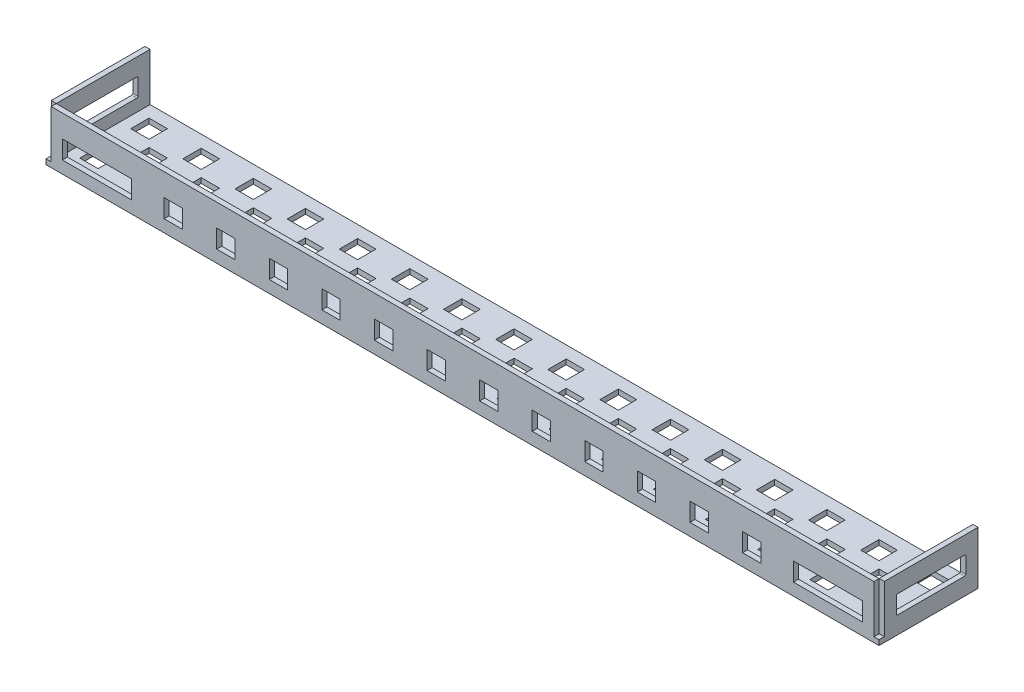
SolidWorks part; units mm, degrees
ref_plane "Front Plane" through (0, 0, 0) normal (0, 0, 1) x (1, 0, 0)
ref_plane "Top Plane" through (0, 0, 0) normal (0, 1, 0) x (1, 0, 0)
ref_plane "Right Plane" through (0, 0, 0) normal (1, 0, 0) x (0, 0, -1)
sketch "Sketch1" plane through (0, 0, 0) normal (0, 1, 0) x (1, 0, 0)
  line L0 (0, 0) -> (0, 23)
  line L1 (0, 23) -> (-204.5, 23)
  line L2 (-204.5, 23) -> (-204.5, 0)
  line L3 (-204.5, 0) -> (0, 0)
  point P13 (0, 0)
  point P14 (0, 0)
  dimension "D1" = 23
  dimension "D2" = 204.5
extrude "Boss-Extrude1" add sketch "Sketch1" along normal blind 1.25
sketch "Sketch2" plane through (0, 1.25, 0) normal (0, 1, 0) x (1, 0, 0)
  line L0 (-204.5, 0) -> (0, 0) construction
  line L1 (-204.5, 23) -> (-203.25, 23)
  line L2 (-204.5, 23) -> (-204.5, 0)
  line L3 (-204.5, 0) -> (-203.25, 0)
  line L4 (-203.25, 23) -> (-203.25, 0)
  line L6 (0, 23) -> (-1.25, 23)
  line L7 (0, 23) -> (0, 0)
  line L8 (0, 0) -> (-1.25, 0)
  line L9 (-1.25, 23) -> (-1.25, 0)
  dimension "D1" = 1.25
  dimension "D2" = 1.25
extrude "Boss-Extrude2" add sketch "Sketch2" along normal blind 11.75
sketch "Sketch3" plane through (0, 0, 0) normal (1, 0, 0) x (0, 0, -1)
  line L0 (0, 13) -> (23, 13) construction
  line L1 (3.25, 8.75) -> (19.75, 8.75)
  line L2 (3, 8.5) -> (3, 4.5)
  line L3 (3.25, 4.25) -> (19.75, 4.25)
  line L4 (20, 8.5) -> (20, 4.5)
  line L5 (0, 13) -> (0, 0) construction
  arc A0 (3.25, 8.75) -> (3, 8.5) centre (3.25, 8.5) ccw
  arc A1 (20, 8.5) -> (19.75, 8.75) centre (19.75, 8.5) ccw
  arc A2 (19.75, 4.25) -> (20, 4.5) centre (19.75, 4.5) ccw
  arc A3 (3.25, 4.25) -> (3, 4.5) centre (3.25, 4.5) cw
  point P4 (11.5, 8.75)
  point P7 (11.5, 13)
  point P8 (3, 6.5)
  point P11 (0, 6.5)
  point P14 (3, 8.75)
  point P17 (20, 8.75)
  dimension "D3" = 0.25
  dimension "D4" = 0.25
  dimension "D1" = 17
  dimension "D2" = 4.5
extrude "Cut-Extrude1" cut sketch "Sketch3" against normal blind 220
sketch "Sketch4" plane through (0, 0, 0) normal (0, -1, 0) x (1, 0, 0)
  line L0 (0, -23) -> (-204.5, -23) construction
  line L1 (-200.5, -3) -> (-196, -3)
  line L2 (-200.5, -3) -> (-200.5, -7.5)
  line L3 (-200.5, -7.5) -> (-196, -7.5)
  line L4 (-196, -3) -> (-196, -7.5)
  line L5 (-200.5, -15.5) -> (-196, -15.5)
  line L6 (-200.5, -15.5) -> (-200.5, -20)
  line L7 (-200.5, -20) -> (-196, -20)
  line L8 (-196, -15.5) -> (-196, -20)
  line L9 (-204.5, -23) -> (-204.5, 0) construction
  line L10 (-187.7, -3) -> (-183.2, -3)
  line L11 (-194.25, -9.25) -> (-189.75, -9.25)
  line L12 (-194.25, -9.25) -> (-194.25, -13.75)
  line L13 (-194.25, -13.75) -> (-189.75, -13.75)
  line L14 (-189.75, -9.25) -> (-189.75, -13.75)
  line L15 (-187.7, -3) -> (-187.7, -7.5)
  line L16 (-187.7, -7.5) -> (-183.2, -7.5)
  line L17 (-183.2, -3) -> (-183.2, -7.5)
  line L18 (-187.7, -15.5) -> (-183.2, -15.5)
  line L19 (-187.7, -15.5) -> (-187.7, -20)
  line L20 (-187.7, -20) -> (-183.2, -20)
  line L21 (-183.2, -15.5) -> (-183.2, -20)
  line L22 (-181.45, -9.25) -> (-176.95, -9.25)
  line L23 (-181.45, -9.25) -> (-181.45, -13.75)
  line L24 (-181.45, -13.75) -> (-176.95, -13.75)
  line L25 (-176.95, -9.25) -> (-176.95, -13.75)
  line L26 (-174.9, -3) -> (-170.4, -3)
  line L27 (-174.9, -3) -> (-174.9, -7.5)
  line L28 (-174.9, -7.5) -> (-170.4, -7.5)
  line L29 (-170.4, -3) -> (-170.4, -7.5)
  line L30 (-174.9, -15.5) -> (-170.4, -15.5)
  line L31 (-174.9, -15.5) -> (-174.9, -20)
  line L32 (-174.9, -20) -> (-170.4, -20)
  line L33 (-170.4, -15.5) -> (-170.4, -20)
  line L34 (-168.65, -9.25) -> (-164.15, -9.25)
  line L35 (-168.65, -9.25) -> (-168.65, -13.75)
  line L36 (-168.65, -13.75) -> (-164.15, -13.75)
  line L37 (-164.15, -9.25) -> (-164.15, -13.75)
  line L38 (-162.1, -3) -> (-157.6, -3)
  line L39 (-162.1, -3) -> (-162.1, -7.5)
  line L40 (-162.1, -7.5) -> (-157.6, -7.5)
  line L41 (-157.6, -3) -> (-157.6, -7.5)
  line L42 (-162.1, -15.5) -> (-157.6, -15.5)
  line L43 (-162.1, -15.5) -> (-162.1, -20)
  line L44 (-162.1, -20) -> (-157.6, -20)
  line L45 (-157.6, -15.5) -> (-157.6, -20)
  line L46 (-155.85, -9.25) -> (-151.35, -9.25)
  line L47 (-155.85, -9.25) -> (-155.85, -13.75)
  line L48 (-155.85, -13.75) -> (-151.35, -13.75)
  line L49 (-151.35, -9.25) -> (-151.35, -13.75)
  line L50 (-149.3, -3) -> (-144.8, -3)
  line L51 (-149.3, -3) -> (-149.3, -7.5)
  line L52 (-149.3, -7.5) -> (-144.8, -7.5)
  line L53 (-144.8, -3) -> (-144.8, -7.5)
  line L54 (-149.3, -15.5) -> (-144.8, -15.5)
  line L55 (-149.3, -15.5) -> (-149.3, -20)
  line L56 (-149.3, -20) -> (-144.8, -20)
  line L57 (-144.8, -15.5) -> (-144.8, -20)
  line L58 (-143.05, -9.25) -> (-138.55, -9.25)
  line L59 (-143.05, -9.25) -> (-143.05, -13.75)
  line L60 (-143.05, -13.75) -> (-138.55, -13.75)
  line L61 (-138.55, -9.25) -> (-138.55, -13.75)
  line L62 (-136.5, -3) -> (-132, -3)
  line L63 (-136.5, -3) -> (-136.5, -7.5)
  line L64 (-136.5, -7.5) -> (-132, -7.5)
  line L65 (-132, -3) -> (-132, -7.5)
  line L66 (-136.5, -15.5) -> (-132, -15.5)
  line L67 (-136.5, -15.5) -> (-136.5, -20)
  line L68 (-136.5, -20) -> (-132, -20)
  line L69 (-132, -15.5) -> (-132, -20)
  line L70 (-130.25, -9.25) -> (-125.75, -9.25)
  line L71 (-130.25, -9.25) -> (-130.25, -13.75)
  line L72 (-130.25, -13.75) -> (-125.75, -13.75)
  line L73 (-125.75, -9.25) -> (-125.75, -13.75)
  line L74 (-123.7, -3) -> (-119.2, -3)
  line L75 (-123.7, -3) -> (-123.7, -7.5)
  line L76 (-123.7, -7.5) -> (-119.2, -7.5)
  line L77 (-119.2, -3) -> (-119.2, -7.5)
  line L78 (-123.7, -15.5) -> (-119.2, -15.5)
  line L79 (-123.7, -15.5) -> (-123.7, -20)
  line L80 (-123.7, -20) -> (-119.2, -20)
  line L81 (-119.2, -15.5) -> (-119.2, -20)
  line L82 (-117.45, -9.25) -> (-112.95, -9.25)
  line L83 (-117.45, -9.25) -> (-117.45, -13.75)
  line L84 (-117.45, -13.75) -> (-112.95, -13.75)
  line L85 (-112.95, -9.25) -> (-112.95, -13.75)
  line L86 (-110.9, -3) -> (-106.4, -3)
  line L87 (-110.9, -3) -> (-110.9, -7.5)
  line L88 (-110.9, -7.5) -> (-106.4, -7.5)
  line L89 (-106.4, -3) -> (-106.4, -7.5)
  line L90 (-110.9, -15.5) -> (-106.4, -15.5)
  line L91 (-110.9, -15.5) -> (-110.9, -20)
  line L92 (-110.9, -20) -> (-106.4, -20)
  line L93 (-106.4, -15.5) -> (-106.4, -20)
  line L94 (-104.65, -9.25) -> (-100.15, -9.25)
  line L95 (-104.65, -9.25) -> (-104.65, -13.75)
  line L96 (-104.65, -13.75) -> (-100.15, -13.75)
  line L97 (-100.15, -9.25) -> (-100.15, -13.75)
  line L98 (-98.1, -3) -> (-93.6, -3)
  line L99 (-98.1, -3) -> (-98.1, -7.5)
  line L100 (-98.1, -7.5) -> (-93.6, -7.5)
  line L101 (-93.6, -3) -> (-93.6, -7.5)
  line L102 (-98.1, -15.5) -> (-93.6, -15.5)
  line L103 (-98.1, -15.5) -> (-98.1, -20)
  line L104 (-98.1, -20) -> (-93.6, -20)
  line L105 (-93.6, -15.5) -> (-93.6, -20)
  line L106 (-91.85, -9.25) -> (-87.35, -9.25)
  line L107 (-91.85, -9.25) -> (-91.85, -13.75)
  line L108 (-91.85, -13.75) -> (-87.35, -13.75)
  line L109 (-87.35, -9.25) -> (-87.35, -13.75)
  line L110 (-85.3, -3) -> (-80.8, -3)
  line L111 (-85.3, -3) -> (-85.3, -7.5)
  line L112 (-85.3, -7.5) -> (-80.8, -7.5)
  line L113 (-80.8, -3) -> (-80.8, -7.5)
  line L114 (-85.3, -15.5) -> (-80.8, -15.5)
  line L115 (-85.3, -15.5) -> (-85.3, -20)
  line L116 (-85.3, -20) -> (-80.8, -20)
  line L117 (-80.8, -15.5) -> (-80.8, -20)
  line L118 (-79.05, -9.25) -> (-74.55, -9.25)
  line L119 (-79.05, -9.25) -> (-79.05, -13.75)
  line L120 (-79.05, -13.75) -> (-74.55, -13.75)
  line L121 (-74.55, -9.25) -> (-74.55, -13.75)
  line L122 (-72.5, -3) -> (-68, -3)
  line L123 (-72.5, -3) -> (-72.5, -7.5)
  line L124 (-72.5, -7.5) -> (-68, -7.5)
  line L125 (-68, -3) -> (-68, -7.5)
  line L126 (-72.5, -15.5) -> (-68, -15.5)
  line L127 (-72.5, -15.5) -> (-72.5, -20)
  line L128 (-72.5, -20) -> (-68, -20)
  line L129 (-68, -15.5) -> (-68, -20)
  line L130 (-66.25, -9.25) -> (-61.75, -9.25)
  line L131 (-66.25, -9.25) -> (-66.25, -13.75)
  line L132 (-66.25, -13.75) -> (-61.75, -13.75)
  line L133 (-61.75, -9.25) -> (-61.75, -13.75)
  line L134 (-59.7, -3) -> (-55.2, -3)
  line L135 (-59.7, -3) -> (-59.7, -7.5)
  line L136 (-59.7, -7.5) -> (-55.2, -7.5)
  line L137 (-55.2, -3) -> (-55.2, -7.5)
  line L138 (-59.7, -15.5) -> (-55.2, -15.5)
  line L139 (-59.7, -15.5) -> (-59.7, -20)
  line L140 (-59.7, -20) -> (-55.2, -20)
  line L141 (-55.2, -15.5) -> (-55.2, -20)
  line L142 (-53.45, -9.25) -> (-48.95, -9.25)
  line L143 (-53.45, -9.25) -> (-53.45, -13.75)
  line L144 (-53.45, -13.75) -> (-48.95, -13.75)
  line L145 (-48.95, -9.25) -> (-48.95, -13.75)
  line L146 (-46.9, -3) -> (-42.4, -3)
  line L147 (-46.9, -3) -> (-46.9, -7.5)
  line L148 (-46.9, -7.5) -> (-42.4, -7.5)
  line L149 (-42.4, -3) -> (-42.4, -7.5)
  line L150 (-46.9, -15.5) -> (-42.4, -15.5)
  line L151 (-46.9, -15.5) -> (-46.9, -20)
  line L152 (-46.9, -20) -> (-42.4, -20)
  line L153 (-42.4, -15.5) -> (-42.4, -20)
  line L154 (-40.65, -9.25) -> (-36.15, -9.25)
  line L155 (-40.65, -9.25) -> (-40.65, -13.75)
  line L156 (-40.65, -13.75) -> (-36.15, -13.75)
  line L157 (-36.15, -9.25) -> (-36.15, -13.75)
  line L158 (-34.1, -3) -> (-29.6, -3)
  line L159 (-34.1, -3) -> (-34.1, -7.5)
  line L160 (-34.1, -7.5) -> (-29.6, -7.5)
  line L161 (-29.6, -3) -> (-29.6, -7.5)
  line L162 (-34.1, -15.5) -> (-29.6, -15.5)
  line L163 (-34.1, -15.5) -> (-34.1, -20)
  line L164 (-34.1, -20) -> (-29.6, -20)
  line L165 (-29.6, -15.5) -> (-29.6, -20)
  line L166 (-27.85, -9.25) -> (-23.35, -9.25)
  line L167 (-27.85, -9.25) -> (-27.85, -13.75)
  line L168 (-27.85, -13.75) -> (-23.35, -13.75)
  line L169 (-23.35, -9.25) -> (-23.35, -13.75)
  line L170 (-21.3, -3) -> (-16.8, -3)
  line L171 (-21.3, -3) -> (-21.3, -7.5)
  line L172 (-21.3, -7.5) -> (-16.8, -7.5)
  line L173 (-16.8, -3) -> (-16.8, -7.5)
  line L174 (-21.3, -15.5) -> (-16.8, -15.5)
  line L175 (-21.3, -15.5) -> (-21.3, -20)
  line L176 (-21.3, -20) -> (-16.8, -20)
  line L177 (-16.8, -15.5) -> (-16.8, -20)
  line L178 (-15.05, -9.25) -> (-10.55, -9.25)
  line L179 (-15.05, -9.25) -> (-15.05, -13.75)
  line L180 (-15.05, -13.75) -> (-10.55, -13.75)
  line L181 (-10.55, -9.25) -> (-10.55, -13.75)
  line L182 (-8.5, -3) -> (-4, -3)
  line L183 (-8.5, -3) -> (-8.5, -7.5)
  line L184 (-8.5, -7.5) -> (-4, -7.5)
  line L185 (-4, -3) -> (-4, -7.5)
  line L186 (-8.5, -15.5) -> (-4, -15.5)
  line L187 (-8.5, -15.5) -> (-8.5, -20)
  line L188 (-8.5, -20) -> (-4, -20)
  line L189 (-4, -15.5) -> (-4, -20)
  line L194 (0, 0) -> (0, -23) construction
  line L195 (-2.25, -9.25) -> (2.25, -9.25) [skipped]
  line L196 (-2.25, -9.25) -> (-2.25, -13.75) [skipped]
  line L197 (-2.25, -13.75) -> (2.25, -13.75) [skipped]
  line L198 (2.25, -9.25) -> (2.25, -13.75) [skipped]
  point P8 (-194.25, -11.5)
  point P9 (-198.25, -15.5)
  point P195 (0, 0)
  point P196 (0, 0)
  dimension "D1" = 4.5
  dimension "D2" = 3
  dimension "D3" = 8
  dimension "D4" = 4
  dimension "D5" = 4
  dimension "D6" = 4
  dimension "D8" = 4
  dimension "D7" = 16
extrude "Cut-Extrude2" cut sketch "Sketch4" against normal blind 220
sketch "Sketch5" plane through (0, 0, 0) normal (0, -1, 0) x (1, 0, 0)
  line L0 (-204.5, 0.05) -> (0, 0.05)
  line L1 (-204.5, 0) -> (0, 0)
  line L2 (-204.5, 0) -> (-204.5, 1.3)
  line L3 (-204.5, 1.3) -> (0, 1.3)
  line L4 (0, 0) -> (0, 1.3)
  dimension "D1" = 1.3
  dimension "D2" = 0.05
extrude "Boss-Extrude4" add sketch "Sketch5" against normal blind 13 separate body contours L0 L4 L3 L2
sketch "Sketch6" plane through (0, 0, 0) normal (0, -1, 0) x (1, 0, 0)
  line L0 (-204.5, 0.05) -> (-204.5, 0)
  line L1 (-204.5, 0) -> (0, 0)
  line L2 (0, 0) -> (0, 0.05)
  line L3 (0, 0.05) -> (-204.5, 0.05)
extrude "Boss-Extrude5" add sketch "Sketch6" against normal blind 1.25
sketch "Sketch7" plane through (0, 0, 1.3) normal (0, 0, 1) x (1, 0, 0)
  line L0 (-204.5, 13) -> (-204.5, 0) construction
  line L1 (-200.5, 7.5) -> (-183.5, 7.5)
  line L2 (-200.5, 7.5) -> (-200.5, 3)
  line L3 (-200.5, 3) -> (-183.5, 3)
  line L4 (-183.5, 7.5) -> (-183.5, 3)
  line L5 (-204.5, 0) -> (0, 0) construction
  line L6 (-102.25, 13) -> (-102.25, 92.5171) construction
  line L8 (-21, 7.5) -> (-21, 3)
  line L9 (-4, 3) -> (-21, 3)
  line L10 (-4, 7.5) -> (-4, 3)
  line L11 (-4, 7.5) -> (-21, 7.5)
  line L12 (-162.5909, 7.5) -> (-158.0909, 7.5)
  line L13 (-175.5, 7.5) -> (-171, 7.5)
  line L14 (-175.5, 7.5) -> (-175.5, 3)
  line L15 (-175.5, 3) -> (-171, 3)
  line L16 (-171, 7.5) -> (-171, 3)
  line L17 (-162.5909, 7.5) -> (-162.5909, 3)
  line L18 (-162.5909, 3) -> (-158.0909, 3)
  line L19 (-158.0909, 7.5) -> (-158.0909, 3)
  line L20 (-149.6818, 7.5) -> (-145.1818, 7.5)
  line L21 (-149.6818, 7.5) -> (-149.6818, 3)
  line L22 (-149.6818, 3) -> (-145.1818, 3)
  line L23 (-145.1818, 7.5) -> (-145.1818, 3)
  line L24 (-136.7727, 7.5) -> (-132.2727, 7.5)
  line L25 (-136.7727, 7.5) -> (-136.7727, 3)
  line L26 (-136.7727, 3) -> (-132.2727, 3)
  line L27 (-132.2727, 7.5) -> (-132.2727, 3)
  line L28 (-123.8636, 7.5) -> (-119.3636, 7.5)
  line L29 (-123.8636, 7.5) -> (-123.8636, 3)
  line L30 (-123.8636, 3) -> (-119.3636, 3)
  line L31 (-119.3636, 7.5) -> (-119.3636, 3)
  line L32 (-110.9545, 7.5) -> (-106.4545, 7.5)
  line L33 (-110.9545, 7.5) -> (-110.9545, 3)
  line L34 (-110.9545, 3) -> (-106.4545, 3)
  line L35 (-106.4545, 7.5) -> (-106.4545, 3)
  line L36 (-98.0455, 7.5) -> (-93.5455, 7.5)
  line L37 (-98.0455, 7.5) -> (-98.0455, 3)
  line L38 (-98.0455, 3) -> (-93.5455, 3)
  line L39 (-93.5455, 7.5) -> (-93.5455, 3)
  line L40 (-85.1364, 7.5) -> (-80.6364, 7.5)
  line L41 (-85.1364, 7.5) -> (-85.1364, 3)
  line L42 (-85.1364, 3) -> (-80.6364, 3)
  line L43 (-80.6364, 7.5) -> (-80.6364, 3)
  line L44 (-72.2273, 7.5) -> (-67.7273, 7.5)
  line L45 (-72.2273, 7.5) -> (-72.2273, 3)
  line L46 (-72.2273, 3) -> (-67.7273, 3)
  line L47 (-67.7273, 7.5) -> (-67.7273, 3)
  line L48 (-59.3182, 7.5) -> (-54.8182, 7.5)
  line L49 (-59.3182, 7.5) -> (-59.3182, 3)
  line L50 (-59.3182, 3) -> (-54.8182, 3)
  line L51 (-54.8182, 7.5) -> (-54.8182, 3)
  line L52 (-46.4091, 7.5) -> (-41.9091, 7.5)
  line L53 (-46.4091, 7.5) -> (-46.4091, 3)
  line L54 (-46.4091, 3) -> (-41.9091, 3)
  line L55 (-41.9091, 7.5) -> (-41.9091, 3)
  line L56 (-33.5, 7.5) -> (-29, 7.5)
  line L57 (-33.5, 7.5) -> (-33.5, 3)
  line L58 (-33.5, 3) -> (-29, 3)
  line L59 (-29, 7.5) -> (-29, 3)
  point P21 (0, 0)
  point P22 (0, 0)
  dimension "D1" = 4.5
  dimension "D2" = 17
  dimension "D3" = 4
  dimension "D4" = 3
  dimension "D5" = 4
  dimension "D6" = 4.5
  dimension "D7" = 8
  dimension "D9" = 8
  dimension "D8" = 12
extrude "Cut-Extrude3" cut sketch "Sketch7" against normal blind 1.25
sketch "Sketch8" plane through (0, 0, 1.3) normal (0, 0, 1) x (1, 0, 0)
  line L0 (-204.5, 0) -> (0, 0) construction
  line L1 (-204.5, 13) -> (-203.25, 13)
  line L2 (-204.5, 13) -> (-204.5, 0)
  line L3 (-204.5, 0) -> (-203.25, 0)
  line L4 (-203.25, 13) -> (-203.25, 0)
  line L6 (0, 13) -> (-1.25, 13)
  line L7 (0, 13) -> (0, 0)
  line L8 (0, 0) -> (-1.25, 0)
  line L9 (-1.25, 13) -> (-1.25, 0)
  dimension "D1" = 1.25
  dimension "D2" = 1.25
extrude "Cut-Extrude4" cut sketch "Sketch8" against normal blind 1.25
sketch "Sketch9" plane through (0, 0, 0) normal (0, -1, 0) x (-1, 0, 0)
  line L0 (203.25, -1.3) -> (1.25, -1.3) construction
  line L1 (1.25, -0.05) -> (0, -0.05)
  line L2 (1.25, -0.05) -> (1.25, -1.3)
  line L3 (1.25, -1.3) -> (0, -1.3)
  line L4 (0, -0.05) -> (0, -1.3)
  line L5 (0, -0.05) -> (0, 23) construction
  line L7 (203.25, -0.05) -> (204.5, -0.05)
  line L8 (203.25, -0.05) -> (203.25, -1.3)
  line L9 (203.25, -1.3) -> (204.5, -1.3)
  line L10 (204.5, -0.05) -> (204.5, -1.3)
  point P5 (0, 0)
extrude "Boss-Extrude6" add sketch "Sketch9" against normal blind 1.25
